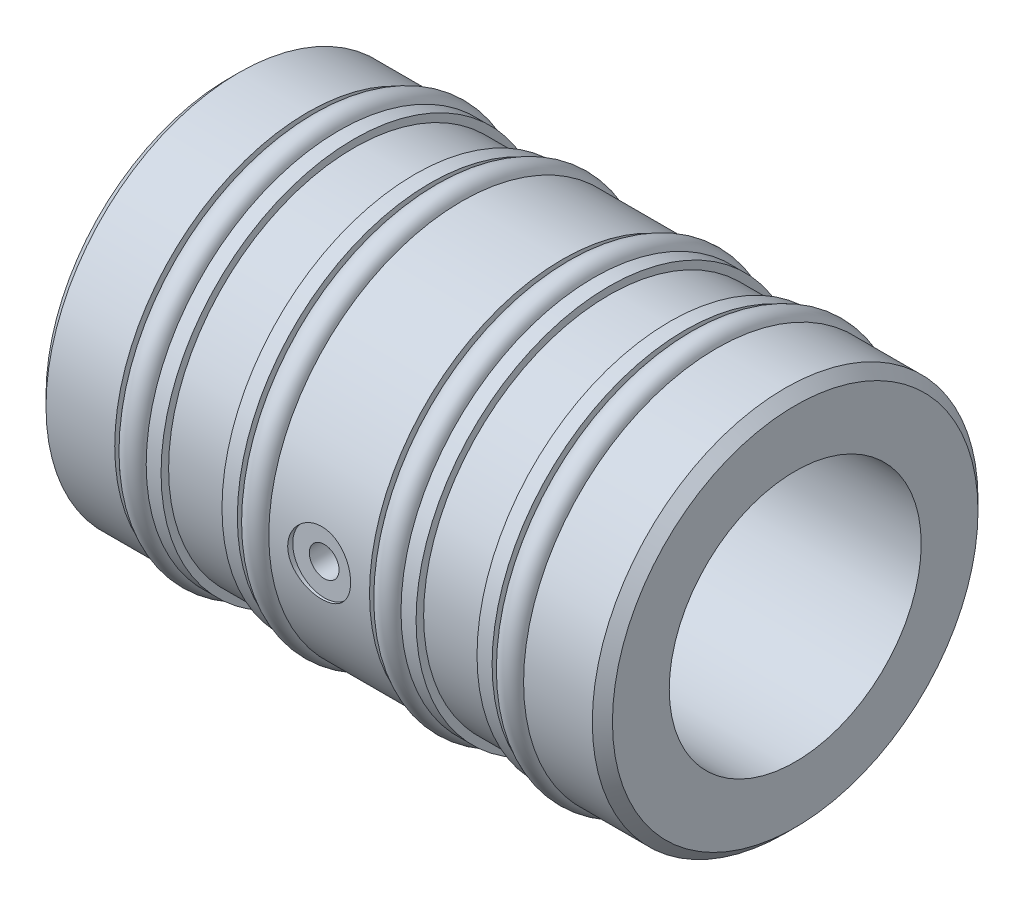
SolidWorks part; units mm, degrees
ref_plane "Front Plane" through (0, 0, 0) normal (0, 0, 1) x (1, 0, 0)
ref_plane "Top Plane" through (0, 0, 0) normal (0, 1, 0) x (1, 0, 0)
ref_plane "Right Plane" through (0, 0, 0) normal (1, 0, 0) x (0, 0, -1)
sketch "Sketch1" plane through (0, 0, 0) normal (0, 0, 1) x (1, 0, 0)
  line L0 (0, 12.7102) -> (57.15, 12.7102)
  line L1 (57.15, 12.7102) -> (57.15, 19.4564)
  line L2 (57.15, 19.4564) -> (49.1998, 19.4564)
  line L3 (49.1998, 19.4564) -> (49.1998, 17.4752)
  line L4 (49.1998, 17.4752) -> (46.0248, 17.4752)
  line L5 (46.0248, 17.4752) -> (46.0248, 19.4564)
  line L6 (46.0248, 19.4564) -> (44.5008, 19.4564)
  line L7 (44.5008, 19.4564) -> (44.5008, 18.6944)
  line L8 (0, 12.7102) -> (0, 19.4564)
  line L9 (0, 19.4564) -> (7.9502, 19.4564)
  line L10 (7.9502, 19.4564) -> (7.9502, 17.4752)
  line L11 (7.9502, 17.4752) -> (11.1252, 17.4752)
  line L12 (11.1252, 17.4752) -> (11.1252, 19.4564)
  line L13 (11.1252, 19.4564) -> (12.6238, 19.4564)
  line L14 (12.6238, 19.4564) -> (12.6238, 18.6944)
  line L15 (12.6238, 18.6944) -> (18.7706, 18.6944)
  line L16 (18.7706, 18.6944) -> (18.7706, 19.4564)
  line L17 (18.7706, 19.4564) -> (20.32, 19.4564)
  line L18 (20.32, 19.4564) -> (20.32, 17.4752)
  line L19 (20.32, 17.4752) -> (23.495, 17.4752)
  line L20 (23.495, 17.4752) -> (23.495, 19.4564)
  line L21 (23.495, 19.4564) -> (33.655, 19.4564)
  line L22 (33.655, 19.4564) -> (33.655, 17.4752)
  line L23 (44.5008, 18.6944) -> (38.354, 18.6944)
  line L24 (38.354, 18.6944) -> (38.354, 19.4564)
  line L25 (38.354, 19.4564) -> (36.83, 19.4564)
  line L26 (36.83, 19.4564) -> (36.83, 17.4752)
  line L27 (36.83, 17.4752) -> (33.655, 17.4752)
  line L28 (0, 0) -> (57.15, 0) construction
  dimension "Bore ID" = 25.4203
  dimension "OAL" = 57.15
  dimension "Moglice groove width" = 6.1468
  dimension "O-ring groove width" = 3.175
  dimension "Edge to 1st o-ring groove" = 7.9502
  dimension "Edge to 2nd o-ring groove" = 20.32
  dimension "Bushing OD" = 38.9128
  dimension "O-ring groove dia" = 34.9504
  dimension "Edge to 3rd o-ring groove" = 33.655
  dimension "edge to 4th o-ring groove" = 46.0248
  dimension "Edge to 1st moglice groove" = 12.6238
  dimension "Edge to 2nd moglice groove" = 38.354
  dimension "Moglice Groove Dia" = 37.3888
revolve "Revolve1" add sketch "Sketch1" angle 360 about L28
chamfer "Chamfer1" distance 1.016 angle 45 2 edges at (0, 0, 19.4564) (57.15, 0, 19.4564)
ref_plane "Plane1" through (0, 0, -7.9121) normal (0, 0, 1) x (1, 0, 0)
hole_wizard "1/4 (0.25) Diameter Hole1" positions "3DSketch1" profile "Sketch2" hole size "1/4" standard "Ansi Inch"
sketch3d "3DSketch1"
  point P0 (28.575, 0, 19.4564)
  dimension "Edge to air hole" = 28.575
sketch "Sketch2" plane through (28.575, 0, 19.4564) normal (1, 0, 0) x (0, -1, 0)
  line L0 (0, 0) -> (0, 0.508)
  line L1 (0, 0.508) -> (3.175, 0.508)
  line L2 (3.175, 0.508) -> (3.175, 0)
  line L5 (3.175, 0) -> (0, 0)
  line L10 (0, 0.508) -> (-3.175, 0.508) construction
  line L11 (0, -6.35) -> (0, 107.95) construction
  dimension "Hole Dia." = 6.35
  dimension "Hole Depth" = 0.508
  dimension "Drill Angle" = 180
hole_wizard "Air Hole" positions "Sketch4" profile "Sketch3" tap size "M3x0.5" standard "Ansi Metric"
sketch "Sketch4" plane through (0, 0, 18.9484) normal (0, 0, 1) x (1, 0, 0)
  circle A0 centre (28.575, 0) radius 3.175 construction
  point P0 (28.575, 0)
sketch "Sketch3" plane through (28.575, 0, 18.9484) normal (1, 0, 0) x (0, -1, 0)
  line L0 (0, 0) -> (0, 7.0978)
  line L1 (0, 7.0978) -> (1.2446, 6.35)
  line L2 (1.2446, 6.35) -> (1.2446, 5.9944)
  line L3 (1.2446, 5.9944) -> (1.4986, 5.9944)
  line L4 (1.4986, 5.9944) -> (1.4986, 0)
  line L5 (1.4986, 0) -> (0, 0)
  line L10 (0, 7.0978) -> (-1.2446, 6.35) construction
  line L11 (0, -6.35) -> (0, 107.95) construction
  dimension "Tap Drill Dia." = 2.4892
  dimension "Tap Drill Depth" = 6.35
  dimension "Thread Major Dia." = 2.9972
  dimension "Thread Depth" = 5.9944
  dimension "Drill Angle" = 118
sketch "Sketch5" plane through (0, 0, 0) normal (0, 0, 1) x (1, 0, 0)
  line L1 (0, 0) -> (57.15, 0) construction
  line L2 (7.9502, 19.4564) -> (7.9502, 17.4752) construction
  line L3 (20.32, 19.4564) -> (20.32, 17.4752) construction
  line L4 (33.655, 19.4564) -> (33.655, 17.4752) construction
  line L5 (46.0248, 17.4752) -> (46.0248, 19.4564) construction
  circle A0 centre (9.5377, 18.7744) radius 1.3018
  circle A1 centre (21.9075, 18.7744) radius 1.3018
  circle A2 centre (35.2425, 18.7744) radius 1.3017
  circle A3 centre (47.6123, 18.7744) radius 1.3017
  dimension "D1" = 2.6035
  dimension "D2" = 20.0762
  dimension "D3" = 1.5875
  dimension "D4" = 1.5875
  dimension "D5" = 1.5875
  dimension "D6" = 1.5875
revolve "Revolve2" add sketch "Sketch5" angle 360 about L28
equation "\"plane offset\"= \"Bushing OD@Sketch1\" / 2"
